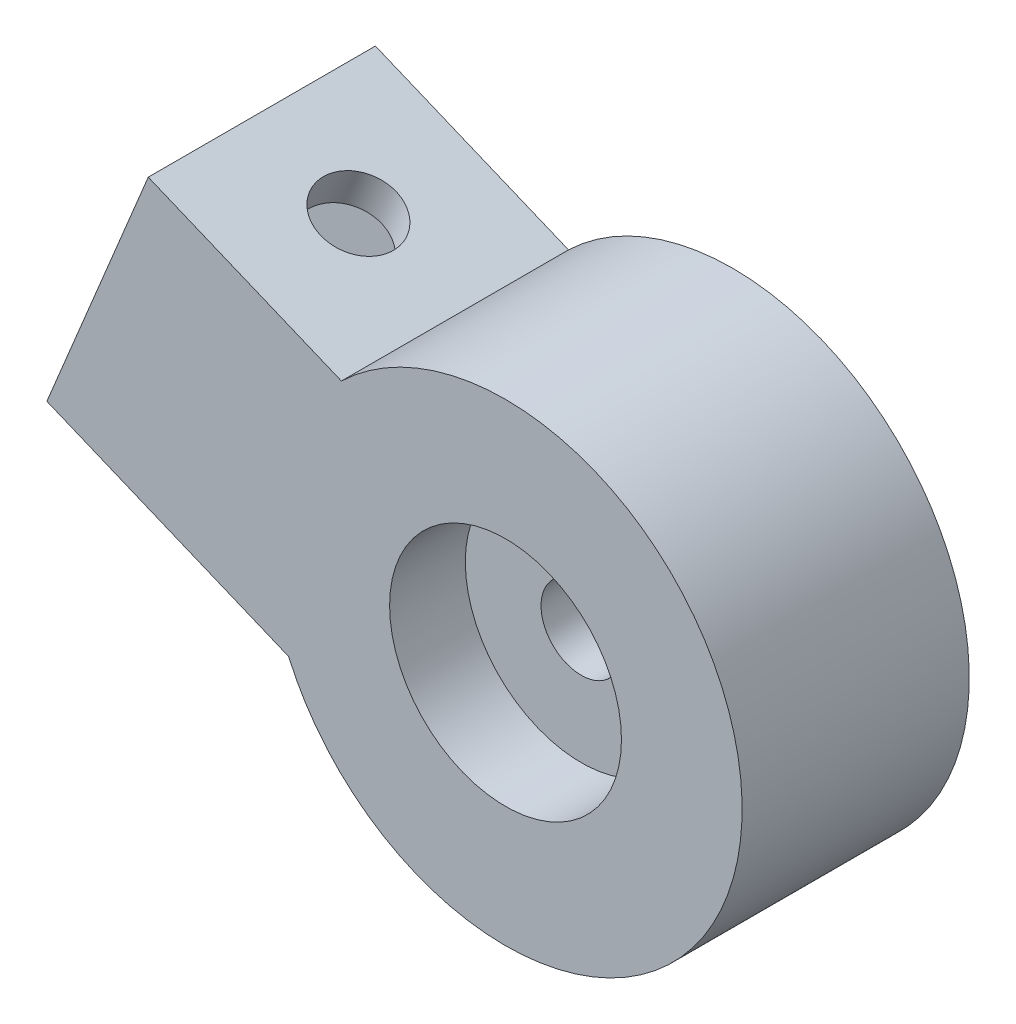
SolidWorks part; units mm, degrees
ref_plane "Front Plane" through (0, 0, 0) normal (0, 0, 1) x (1, 0, 0)
ref_plane "Top Plane" through (0, 0, 0) normal (0, 1, 0) x (1, 0, 0)
ref_plane "Right Plane" through (0, 0, 0) normal (1, 0, 0) x (0, 0, -1)
sketch "Sketch1" plane through (0, 0, 0) normal (0, 0, 1) x (1, 0, 0)
  line L0 (0, 0) -> (-12.5, 0) construction
  line L1 (0, 0) -> (-11.5485, -4.7835) construction
  line L3 (0, 0) -> (0, 10) construction
  line L12 (-20.7873, -8.6104) -> (-11.5485, -4.7835) construction
  line L16 (-20.7873, 8.6104) -> (-18.8739, 13.2298)
  line L20 (-18.8739, 13.2298) -> (-8.671, 9.0036)
  line L21 (-20.7873, 8.6104) -> (-24.2314, 0.2955)
  line L22 (-24.2314, 0.2955) -> (-11.4585, -4.9953)
  circle A3 centre (0, 0) radius 12.5
  circle A4 centre (0, 0) radius 10
  dimension "D1" = 25
  dimension "D3" = 22.5
  dimension "D2" = 20
  dimension "D4" = 10
extrude "Boss-Extrude2" add sketch "Sketch1" along normal blind 12 contours A3
sketch "Sketch2" plane through (0, 0, 0) normal (0, 0, 1) x (1, 0, 0)
  line L0 (-24.2314, 0.2955) -> (-11.4585, -4.9953) construction
  line L1 (-20.7873, 8.6104) -> (-24.2314, 0.2955) construction
  line L2 (-18.8739, 13.2298) -> (-8.671, 9.0036) construction
  line L3 (-20.7873, 8.6104) -> (-18.8739, 13.2298) construction
  line L4 (-24.2314, 0.2955) -> (-11.4585, -4.9953)
  line L5 (-20.7873, 8.6104) -> (-24.2314, 0.2955)
  line L6 (-18.8739, 13.2298) -> (-8.671, 9.0036)
  line L7 (-20.7873, 8.6104) -> (-18.8739, 13.2298)
  circle A0 centre (0, 0) radius 12.5 construction
  arc A1 (-8.671, 9.0036) -> (-11.4585, -4.9953) centre (0, 0) ccw
extrude "Boss-Extrude3" add sketch "Sketch2" along normal blind 12
sketch "Sketch3" plane through (-20.7873, 8.6104, 0) normal (-0.9239, 0.3827, 0) x (0, 0, 1)
  line L0 (12, 5) -> (0, 5) construction
  line L1 (2, 3) -> (10, 3)
  line L2 (2, 3) -> (2, -7)
  line L3 (2, -7) -> (10, -7)
  line L4 (10, 3) -> (10, -7)
  line L5 (12, -9) -> (0, -9) construction
  line L6 (0, 5) -> (0, -9) construction
  line L7 (12, 5) -> (12, -9) construction
  dimension "D1" = 2
  dimension "D2" = 2
  dimension "D3" = 2
  dimension "D4" = 2
extrude "Cut-Extrude1" cut sketch "Sketch3" against normal blind 10
sketch "Sketch4" plane through (1.9134, 4.6194, 0) normal (0.3827, 0.9239, 0) x (0.9239, -0.3827, 0)
  line L0 (-11.4564, -6) -> (-22.5, -6) construction
  line L1 (-11.4564, -12) -> (-11.4564, 0) construction
  line L2 (-22.5, -12) -> (-22.5, 0) construction
  line L3 (-16.9782, 0) -> (-16.9782, -12) construction
  line L4 (-11.4564, 0) -> (-22.5, 0) construction
  line L5 (-11.4564, -12) -> (-22.5, -12) construction
  circle A0 centre (-16.9782, -6) radius 2
extrude "Cut-Extrude2" cut sketch "Sketch4" against normal up to surface (14 mm away) up to face at (-17.845, -2.3499, 6)
sketch "Sketch5" plane through (0, 0, 12) normal (0, 0, 1) x (1, 0, 0)
  line L0 (0, 0) -> (0, 10) construction
  line L1 (0, 0) -> (10, 0) construction
  circle A7 centre (0, 0) radius 6.125
  point P17 (0, 0)
extrude "Cut-Extrude3" cut sketch "Sketch5" against normal blind 4
sketch "Sketch6" plane through (0, 0, 8) normal (0, 0, 1) x (1, 0, 0)
  circle A0 centre (0, 0) radius 2.125
  dimension "D1" = 4.25
extrude "Cut-Extrude4" cut sketch "Sketch6" against normal through all
